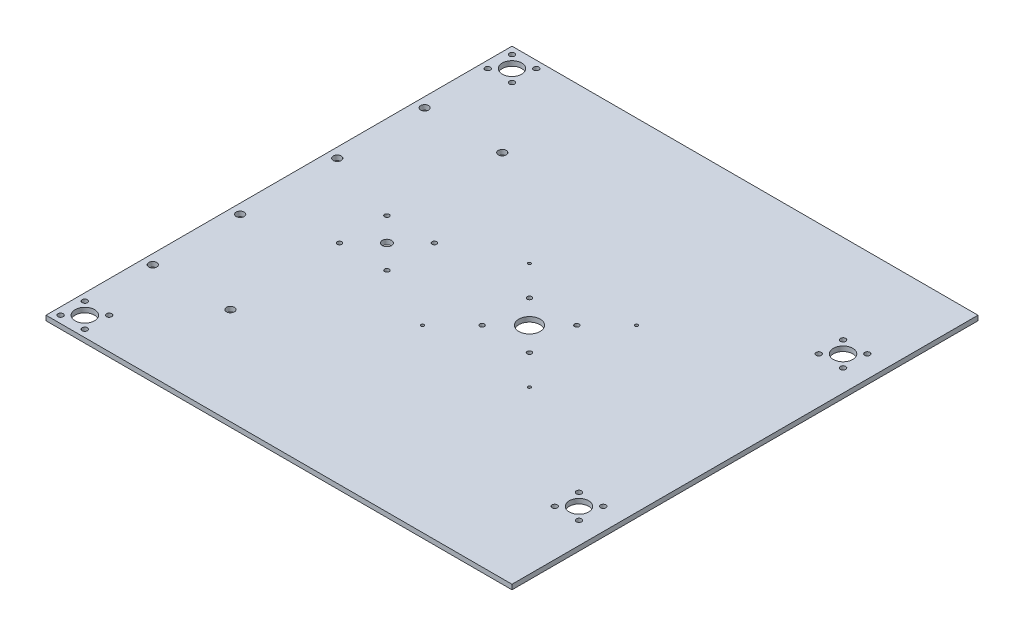
SolidWorks part; units mm, degrees
material "Balsa"
ref_plane "Front Plane" through (0, 0, 0) normal (0, 0, 1) x (1, 0, 0)
ref_plane "Top Plane" through (0, 0, 0) normal (0, 1, 0) x (1, 0, 0)
ref_plane "Right Plane" through (0, 0, 0) normal (1, 0, 0) x (0, 0, -1)
sketch "Sketch1" plane through (0, 0, 0) normal (0, 1, 0) x (1, 0, 0)
  line L1 (-152.4, -152.4) -> (152.4, -152.4)
  line L2 (-152.4, -152.4) -> (-152.4, 152.4)
  line L3 (-152.4, 152.4) -> (152.4, 152.4)
  line L4 (152.4, -152.4) -> (152.4, 152.4)
  line L5 (-152.4, -152.4) -> (152.4, 152.4) construction
  line L6 (-152.4, 152.4) -> (152.4, -152.4) construction
  point P0 (0, 0)
  dimension "D1" = 304.8
  dimension "D2" = 304.8
extrude "Boss-Extrude1" add sketch "Sketch1" along normal blind 3.175
sketch "Sketch2" plane through (0, 0, 0) normal (0, 1, 0) x (1, 0, 0)
  line L0 (-193.2668, 0) -> (192.9727, 0) construction
sketch "Sketch3" plane through (0, 3.175, 0) normal (0, 1, 0) x (1, 0, 0)
  circle A1 centre (-146.05, -31.75) radius 2.6
  circle A2 centre (-146.05, -31.75) radius 2.6
  circle A3 centre (-95.25, -88.9) radius 2.6
  circle A4 centre (-95.25, -88.9) radius 2.6
  circle A5 centre (-146.05, -88.9) radius 2.6
  circle A6 centre (-146.05, -88.9) radius 2.6
  dimension "D1" = 0
  dimension "D2" = 0
  dimension "D3" = 0
sketch "Sketch5" plane through (0, 3.175, 0) normal (0, 1, 0) x (1, 0, 0)
  circle A0 centre (-66.312, 15.5) radius 1.5 construction
  circle A1 centre (-66.312, -15.5) radius 1.5 construction
  circle A2 centre (-97.312, 15.5) radius 1.5 construction
  circle A3 centre (-97.312, -15.5) radius 1.5 construction
  circle A4 centre (-81.812, 0) radius 2.5 construction
  circle A5 centre (-66.312, 15.5) radius 1.5
  circle A6 centre (-66.312, -15.5) radius 1.5
  circle A7 centre (-97.312, 15.5) radius 1.5
  circle A8 centre (-97.312, -15.5) radius 1.5
  circle A9 centre (-81.812, 0) radius 2.5 construction
  circle A10 centre (-81.812, 0) radius 3
  dimension "D1" = 6
sketch "Sketch7" plane through (0, 3.175, 0) normal (0, 1, 0) x (1, 0, 0)
  circle A0 centre (46.4318, -35.0018) radius 1 construction
  circle A1 centre (-23.5718, -35.0018) radius 1 construction
  circle A2 centre (46.4318, -35.0018) radius 1
  circle A3 centre (-23.5718, -35.0018) radius 1
  circle A4 centre (-23.5718, 35.0018) radius 1 construction
  circle A5 centre (46.4318, 35.0018) radius 1 construction
  circle A6 centre (-23.5718, 35.0018) radius 1
  circle A7 centre (46.4318, 35.0018) radius 1
extrude "Cut-Extrude1" cut sketch "Sketch3" against normal through all
mirror "Mirror1" about plane through (0, 0, 0) normal (0, 0, 1) of "Cut-Extrude1"
extrude "Cut-Extrude2" cut sketch "Sketch5" against normal through all
extrude "Cut-Extrude3" cut sketch "Sketch7" against normal through all
sketch "Sketch9" plane through (0, 3.175, 0) normal (0, 1, 0) x (1, 0, 0)
  circle A0 centre (-131.7625, -147.6375) radius 1.727 construction
  circle A1 centre (-131.7625, -131.7625) radius 1.727 construction
  circle A2 centre (-147.6375, -131.7625) radius 1.727 construction
  circle A3 centre (-147.6375, -147.6375) radius 1.727 construction
  circle A4 centre (-139.7, -139.7) radius 6.35 construction
  circle A5 centre (-131.7625, -147.6375) radius 1.727
  circle A6 centre (-131.7625, -131.7625) radius 1.727
  circle A7 centre (-147.6375, -131.7625) radius 1.727
  circle A8 centre (-147.6375, -147.6375) radius 1.727
  circle A9 centre (-139.7, -139.7) radius 6.35
  circle A10 centre (138.1125, -94.2975) radius 1.727 construction
  circle A11 centre (138.1125, -78.4225) radius 1.727 construction
  circle A12 centre (130.175, -86.36) radius 6.35 construction
  circle A13 centre (122.2375, -78.4225) radius 1.727 construction
  circle A14 centre (122.2375, -94.2975) radius 1.727 construction
  circle A15 centre (138.1125, -94.2975) radius 1.727
  circle A16 centre (138.1125, -78.4225) radius 1.727
  circle A17 centre (130.175, -86.36) radius 6.35
  circle A18 centre (122.2375, -78.4225) radius 1.727
  circle A19 centre (122.2375, -94.2975) radius 1.727
  circle A30 centre (122.2375, 94.2975) radius 1.727 construction
  circle A31 centre (122.2375, 78.4225) radius 1.727 construction
  circle A32 centre (138.1125, 94.2975) radius 1.727 construction
  circle A33 centre (130.175, 86.36) radius 6.35 construction
  circle A34 centre (138.1125, 78.4225) radius 1.727 construction
  circle A35 centre (122.2375, 94.2975) radius 1.727
  circle A36 centre (122.2375, 78.4225) radius 1.727
  circle A37 centre (138.1125, 94.2975) radius 1.727
  circle A38 centre (130.175, 86.36) radius 6.35
  circle A39 centre (138.1125, 78.4225) radius 1.727
  circle A40 centre (-131.7625, 131.7625) radius 1.727 construction
  circle A41 centre (-131.7625, 147.6375) radius 1.727 construction
  circle A42 centre (-147.6375, 147.6375) radius 1.727 construction
  circle A43 centre (-147.6375, 131.7625) radius 1.727 construction
  circle A44 centre (-131.7625, 131.7625) radius 1.727
  circle A45 centre (-131.7625, 147.6375) radius 1.727
  circle A46 centre (-147.6375, 147.6375) radius 1.727
  circle A47 centre (-147.6375, 131.7625) radius 1.727
  circle A48 centre (-139.7, 139.7) radius 6.35 construction
  circle A49 centre (-139.7, 139.7) radius 6.35
extrude "Cut-Extrude5" cut sketch "Sketch9" against normal through all both and the other way through all
sketch "Sketch11" plane through (0, 3.175, 0) normal (0, 1, 0) x (1, 0, 0)
  circle A0 centre (26.93, 15.5) radius 1.5 construction
  circle A1 centre (26.93, -15.5) radius 1.5 construction
  circle A2 centre (-4.07, -15.5) radius 1.5 construction
  circle A3 centre (-4.07, 15.5) radius 1.5 construction
  circle A4 centre (11.43, 0) radius 5.25 construction
  circle A5 centre (26.93, 15.5) radius 1.5
  circle A6 centre (26.93, -15.5) radius 1.5
  circle A7 centre (-4.07, -15.5) radius 1.5
  circle A8 centre (-4.07, 15.5) radius 1.5
  circle A9 centre (11.43, 0) radius 5.25 construction
  circle A10 centre (11.43, 0) radius 6.985
  dimension "D1" = 13.97
extrude "Cut-Extrude6" cut sketch "Sketch11" against normal through all both and the other way through all
equation "\"tightTol\"= 0.005in"
equation "\"normTol\"= 0.01in"
equation "\"looseTol\"= 0.02in"
equation "\"D1@Sketch5\"=6mm"
